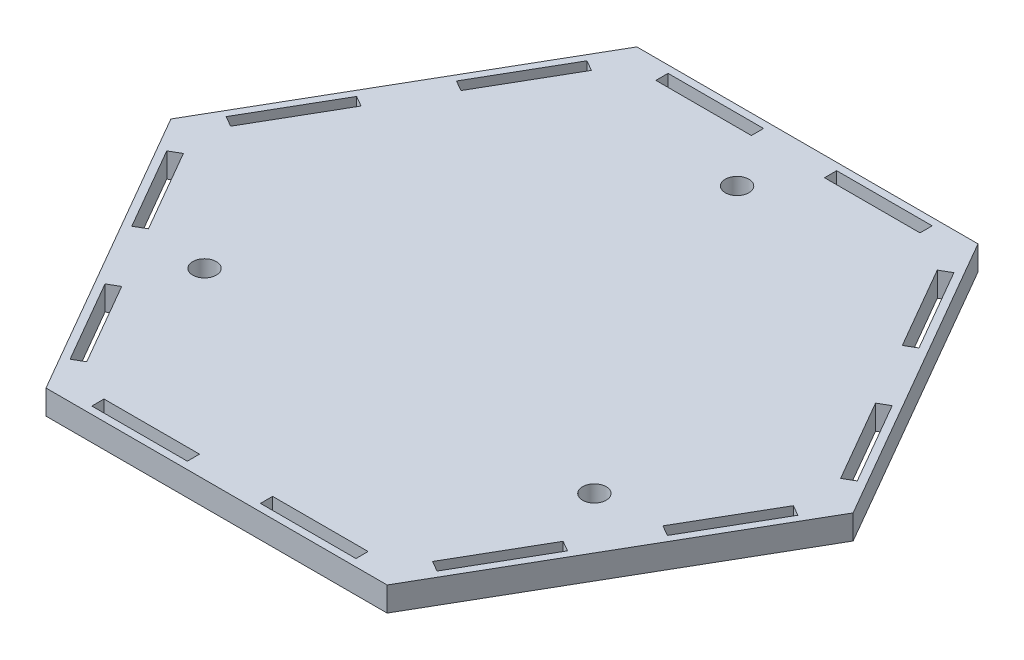
SolidWorks part; units mm, degrees
material "Cedar"
ref_plane "Front Plane" through (0, 0, 0) normal (0, 0, 1) x (1, 0, 0)
ref_plane "Top Plane" through (0, 0, 0) normal (0, 1, 0) x (1, 0, 0)
ref_plane "Right Plane" through (0, 0, 0) normal (1, 0, 0) x (0, 0, -1)
sketch "Sketch1" plane through (0, 0, 0) normal (0, 1, 0) x (1, 0, 0)
  line L0 (-88.9, 0) -> (-44.45, -76.9897)
  line L1 (88.9, 0) -> (44.45, 76.9897)
  line L2 (44.45, 76.9897) -> (-44.45, 76.9897)
  line L3 (-44.45, 76.9897) -> (-88.9, 0)
  line L4 (-44.45, -76.9897) -> (44.45, -76.9897)
  line L5 (44.45, -76.9897) -> (88.9, 0)
  line L6 (0, 0) -> (88.9, 0) construction
  circle A0 centre (0, 0) radius 76.9897 construction
  dimension "D1" = 88.9
extrude "Boss-Extrude1" add sketch "Sketch1" along normal blind 6.35
sketch "Sketch2" plane through (0, 6.35, 0) normal (0, 1, 0) x (1, 0, 0)
  line L0 (0, 0) -> (0, 58.6588) construction
  line L1 (50.8, -29.3294) -> (0, 58.6588) construction
  line L2 (0, 58.6588) -> (-50.8, -29.3294) construction
  line L3 (-50.8, -29.3294) -> (50.8, -29.3294) construction
  line L4 (-85.9671, 5.08) -> (-38.5841, -76.9897) construction
  line L5 (-44.45, 76.9897) -> (-88.9, 0) construction
  line L6 (-44.45, -76.9897) -> (44.45, -76.9897) construction
  line L7 (-88.9, 0) -> (-44.45, -76.9897) construction
  line L8 (-66.675, -38.4948) -> (-62.2756, -35.9548) construction
  line L9 (-79.4841, -6.1488) -> (-82.2337, -7.7363)
  line L10 (-82.2337, -7.7363) -> (-69.7877, -29.2934)
  line L11 (-69.7877, -29.2934) -> (-67.0381, -27.7059)
  line L12 (-67.0381, -27.7059) -> (-79.4841, -6.1488)
  line L13 (-45.0671, -65.7608) -> (-47.8167, -67.3483)
  line L14 (-57.5131, -44.2037) -> (-45.0671, -65.7608)
  line L15 (-47.8167, -67.3483) -> (-60.2627, -45.7912)
  line L16 (-60.2627, -45.7912) -> (-57.5131, -44.2037)
  line L17 (-38.5841, 76.9897) -> (-85.9671, -5.08) construction
  line L18 (-45.0671, 65.7608) -> (-47.8167, 67.3483)
  line L19 (-47.8167, 67.3483) -> (-60.2627, 45.7912)
  line L20 (-57.5131, 44.2037) -> (-45.0671, 65.7608)
  line L21 (-60.2627, 45.7912) -> (-57.5131, 44.2037)
  line L22 (-66.675, 38.4948) -> (-62.2756, 35.9548) construction
  line L23 (-69.7877, 29.2934) -> (-67.0381, 27.7059)
  line L24 (-82.2337, 7.7363) -> (-69.7877, 29.2934)
  line L25 (-67.0381, 27.7059) -> (-79.4841, 6.1488)
  line L26 (-79.4841, 6.1488) -> (-82.2337, 7.7363)
  line L27 (47.3829, 71.9097) -> (-47.3829, 71.9097) construction
  line L28 (34.417, 71.9097) -> (34.417, 75.0847)
  line L29 (34.417, 75.0847) -> (9.525, 75.0847)
  line L30 (9.525, 71.9097) -> (34.417, 71.9097)
  line L31 (9.525, 75.0847) -> (9.525, 71.9097)
  line L32 (0, 76.9897) -> (0, 71.9097) construction
  line L33 (-9.525, 75.0847) -> (-9.525, 71.9097)
  line L34 (-34.417, 75.0847) -> (-9.525, 75.0847)
  line L35 (-9.525, 71.9097) -> (-34.417, 71.9097)
  line L36 (-34.417, 71.9097) -> (-34.417, 75.0847)
  line L37 (85.9671, -5.08) -> (38.5841, 76.9897) construction
  line L38 (79.4841, 6.1488) -> (82.2337, 7.7363)
  line L39 (82.2337, 7.7363) -> (69.7877, 29.2934)
  line L40 (67.0381, 27.7059) -> (79.4841, 6.1488)
  line L41 (69.7877, 29.2934) -> (67.0381, 27.7059)
  line L42 (66.675, 38.4948) -> (62.2756, 35.9548) construction
  line L43 (60.2627, 45.7912) -> (57.5131, 44.2037)
  line L44 (47.8167, 67.3483) -> (60.2627, 45.7912)
  line L45 (57.5131, 44.2037) -> (45.0671, 65.7608)
  line L46 (45.0671, 65.7608) -> (47.8167, 67.3483)
  line L47 (38.5841, -76.9897) -> (85.9671, 5.08) construction
  line L48 (45.0671, -65.7608) -> (47.8167, -67.3483)
  line L49 (47.8167, -67.3483) -> (60.2627, -45.7912)
  line L50 (57.5131, -44.2037) -> (45.0671, -65.7608)
  line L51 (60.2627, -45.7912) -> (57.5131, -44.2037)
  line L52 (66.675, -38.4948) -> (62.2756, -35.9548) construction
  line L53 (69.7877, -29.2934) -> (67.0381, -27.7059)
  line L54 (82.2337, -7.7363) -> (69.7877, -29.2934)
  line L55 (67.0381, -27.7059) -> (79.4841, -6.1488)
  line L56 (79.4841, -6.1488) -> (82.2337, -7.7363)
  line L57 (-47.3829, -71.9097) -> (47.3829, -71.9097) construction
  line L58 (-34.417, -71.9097) -> (-34.417, -75.0847)
  line L59 (-34.417, -75.0847) -> (-9.525, -75.0847)
  line L60 (-9.525, -71.9097) -> (-34.417, -71.9097)
  line L61 (-9.525, -75.0847) -> (-9.525, -71.9097)
  line L62 (0, -76.9897) -> (0, -71.9097) construction
  line L63 (9.525, -75.0847) -> (9.525, -71.9097)
  line L64 (34.417, -75.0847) -> (9.525, -75.0847)
  line L65 (9.525, -71.9097) -> (34.417, -71.9097)
  line L66 (34.417, -71.9097) -> (34.417, -75.0847)
  circle A0 centre (0, 0) radius 29.3294 construction
  circle A1 centre (-50.8, -29.3294) radius 3.0734
  circle A4 centre (0, 58.6588) radius 3.0734
  circle A5 centre (50.8, -29.3294) radius 3.0734
  point P13 (0, 0)
  point P92 (0, 0)
  point P94 (0, 0)
  dimension "D2" = 6.1468
  dimension "D3" = 3
  dimension "D1" = 101.6
  dimension "D4" = 5.08
  dimension "D5" = 3.175
  dimension "D6" = 24.892
  dimension "D7" = 9.525
  dimension "D8" = 6
extrude "Cut-Extrude1" cut sketch "Sketch2" against normal through all
